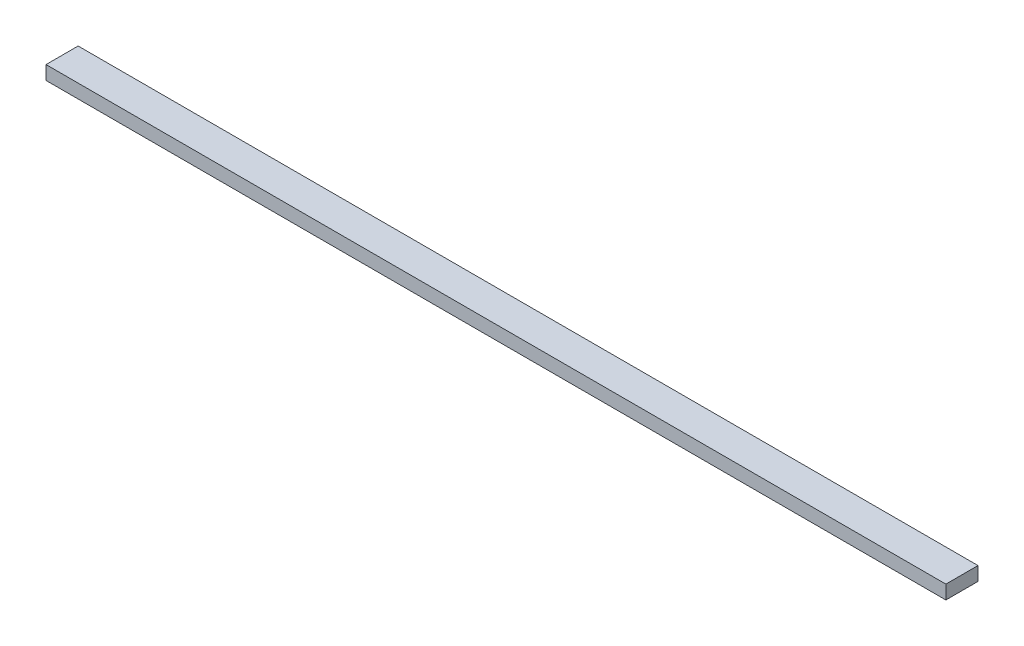
SolidWorks part; units mm, degrees
ref_plane "Front Plane" through (0, 0, 0) normal (0, 0, 1) x (1, 0, 0)
ref_plane "Top Plane" through (0, 0, 0) normal (0, 1, 0) x (1, 0, 0)
ref_plane "Right Plane" through (0, 0, 0) normal (1, 0, 0) x (0, 0, -1)
sketch "Sketch1" plane through (0, 0, 0) normal (0, 1, 0) x (1, 0, 0)
  line L1 (0, 0) -> (2489.2, 0)
  line L2 (0, 0) -> (0, -88.9)
  line L3 (0, -88.9) -> (2489.2, -88.9)
  line L4 (2489.2, 0) -> (2489.2, -88.9)
extrude "Boss-Extrude1" add sketch "Sketch1" along normal blind 38.1
sketch "Sketch2" plane through (0, 38.1, 0) normal (0, 1, 0) x (1, 0, 0)
  line L0 (0, -44.45) -> (829.7333, -44.45) construction
  line L1 (0, 0) -> (0, -88.9) construction
  line L2 (829.7333, -44.45) -> (1659.4667, -44.45) construction
  line L3 (1659.4667, -44.45) -> (2489.2, -44.45) construction
  line L4 (2489.2, -88.9) -> (2489.2, 0) construction
  line L5 (829.7333, 0) -> (829.7333, -88.9) construction
  line L6 (2489.2, 0) -> (0, 0) construction
  line L7 (0, -88.9) -> (2489.2, -88.9) construction
  line L8 (1659.4667, 0) -> (1659.4667, -88.9) construction
sketch "Sketch3" plane through (0, 0, 0) normal (0, -1, 0) x (1, 0, 0)
  line L0 (0, 44.45) -> (829.7333, 44.45) construction
  line L1 (829.7333, 44.45) -> (1659.4667, 44.45) construction
  line L2 (1659.4667, 44.45) -> (2489.2, 44.45) construction
  line L3 (829.7333, 88.9) -> (829.7333, 0) construction
  line L4 (1659.4667, 88.9) -> (1659.4667, 0) construction
